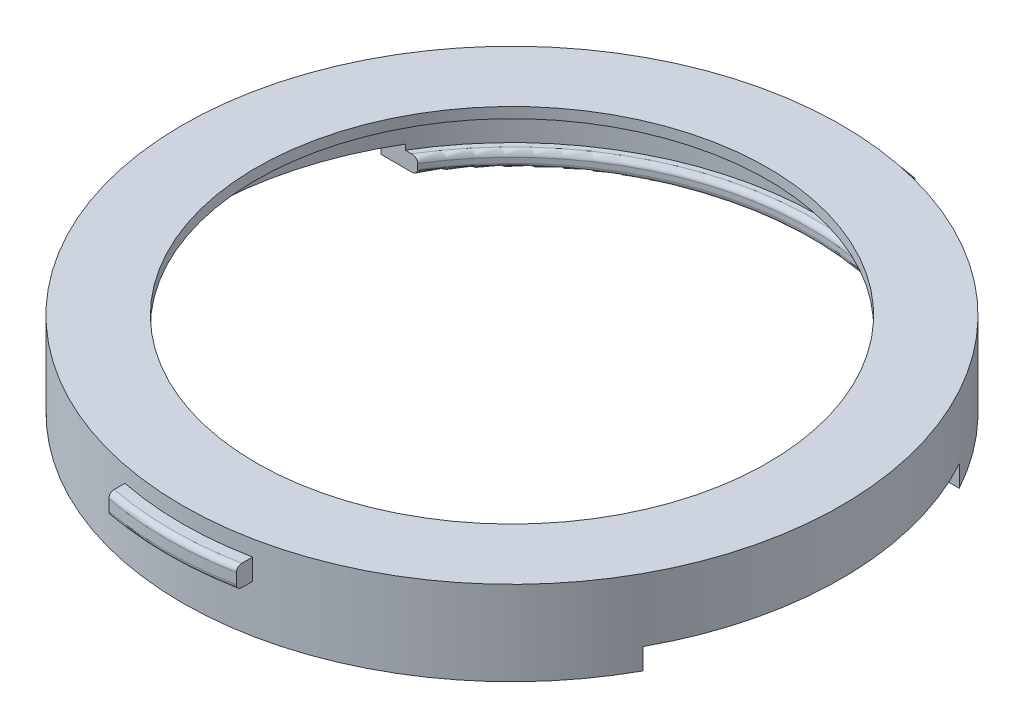
SolidWorks part; units mm, degrees
material "ABS"
ref_plane "Front Plane" through (0, 0, 0) normal (0, 0, 1) x (1, 0, 0)
ref_plane "Top Plane" through (0, 0, 0) normal (0, 1, 0) x (1, 0, 0)
ref_plane "Right Plane" through (0, 0, 0) normal (1, 0, 0) x (0, 0, -1)
sketch "Sketch1" plane through (0, 0, 0) normal (0, 1, 0) x (1, 0, 0)
  circle A0 centre (0, 0) radius 29.25
  circle A1 centre (0, 0) radius 31.25
  dimension "D1" = 58.5
  dimension "D2" = 2
extrude "Boss-Extrude2" add sketch "Sketch1" along normal blind 8
ref_plane "Plane1" through (0, 1.5, 0) normal (0, 1, 0) x (1, 0, 0)
sketch "Sketch3" plane through (0, 1.5, 0) normal (0, 1, 0) x (1, 0, 0)
  circle A0 centre (0, 0) radius 29.25
  circle A1 centre (0, 0) radius 28.25
  circle A2 centre (0, 0) radius 29.25 construction
  dimension "D2" = 1
extrude "Boss-Extrude3" add sketch "Sketch3" against normal blind 1.5
fillet "Fillet1" radius 0.5 2 edges at (0, 1.5, 28.25) (0, 0, 28.25)
sketch "Sketch4" plane through (0, 8, 0) normal (0, 1, 0) x (1, 0, 0)
  circle A0 centre (0, 0) radius 29.25 construction
  circle A1 centre (0, 0) radius 29.25
  circle A2 centre (0, 0) radius 24.25
  dimension "D1" = 5
extrude "Boss-Extrude4" add sketch "Sketch4" against normal blind 1
sketch "Sketch5" plane through (0, 7, 0) normal (0, -1, 0) x (1, 0, 0)
  line L1 (-35, -15) -> (35, -15)
  line L2 (-35, -15) -> (-35, 15)
  line L3 (-35, 15) -> (35, 15)
  line L4 (35, -15) -> (35, 15)
  line L5 (0, 15) -> (0, -15) construction
  line L6 (-35, 0) -> (35, 0) construction
  point P0 (0, 0)
  dimension "D1" = 30
  dimension "D2" = 70
extrude "Cut-Extrude3" cut sketch "Sketch5" along normal up to surface (2 mm away) from offset 5 up to face at (0, 0, 28.75)
ref_plane "Plane2" through (0, 5.5, 0) normal (0, 1, 0) x (1, 0, 0)
sketch "Sketch6" plane through (0, 5.5, 0) normal (0, 1, 0) x (1, 0, 0)
  line L0 (6.051, 30.6586) -> (6.051, 32.1861)
  line L2 (-6.051, 32.1861) -> (-6.051, -32.1861) construction
  line L4 (6.051, 32.1861) -> (6.051, -32.1861) construction
  line L5 (0, -31.25) -> (0, 31.25) construction
  line L6 (-6.051, 0) -> (6.051, 0) construction
  line L7 (-6.051, 30.6586) -> (-6.051, 32.1861)
  line L8 (-6.051, -32.1861) -> (-6.051, -30.6586)
  line L9 (6.051, -32.1861) -> (6.051, -30.6586)
  circle A0 centre (0, 0) radius 31.25 construction
  arc A1 (6.051, 30.6586) -> (-6.051, 30.6586) centre (0, 0) ccw
  arc A2 (6.051, 32.1861) -> (-6.051, 32.1861) centre (0, 0) ccw
  circle A3 centre (0, 0) radius 32.75 construction
  circle A4 centre (0, 0) radius 31.25 construction
  arc A5 (-6.051, -32.1861) -> (6.051, -32.1861) centre (0, 0) ccw
  arc A6 (-6.051, -30.6586) -> (6.051, -30.6586) centre (0, 0) ccw
  point P12 (0, 0)
  dimension "D2" = 12.1021
  dimension "D1" = 1.5
extrude "Boss-Extrude5" add sketch "Sketch6" along normal blind 1 and the other way blind 1
fillet "Fillet3" radius 0.5 4 edges at (0, 6.5, -32.75) (0, 4.5, -32.75) (0, 4.5, 32.75) (0, 6.5, 32.75)
